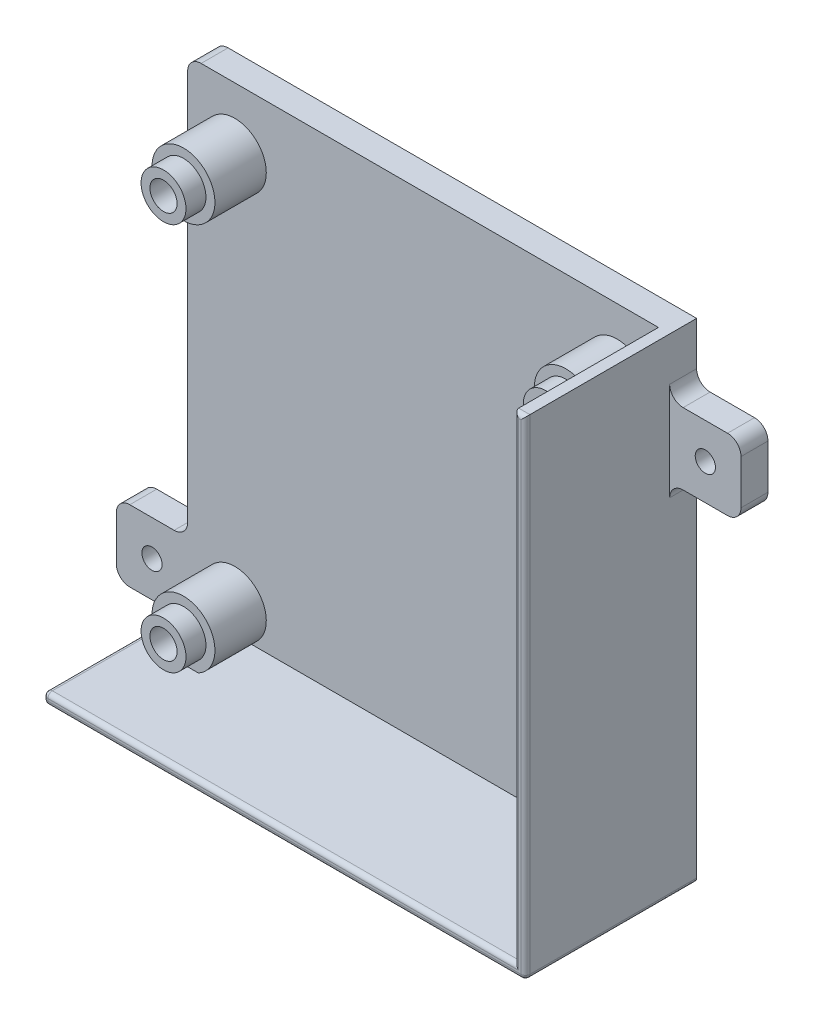
SolidWorks part; units mm, degrees
material "ABS"
ref_plane "X-Y Datum" through (0, 0, 0) normal (0, 0, 1) x (1, 0, 0)
ref_plane "X-Z Datum" through (0, 0, 0) normal (0, 1, 0) x (1, 0, 0)
ref_plane "Y-Z Datum" through (0, 0, 0) normal (1, 0, 0) x (0, 0, -1)
sketch "Sketch1" plane through (0, 0, 0) normal (0, 0, 1) x (1, 0, 0)
  line L1 (-52.3875, 53.1812) -> (52.3875, 53.1812)
  line L2 (-52.3875, 53.1812) -> (-52.3875, -53.1812)
  line L3 (-52.3875, -53.1812) -> (52.3875, -53.1812)
  line L4 (52.3875, 53.1812) -> (52.3875, -53.1812)
  line L5 (-52.3875, 53.1812) -> (52.3875, -53.1812) construction
  line L6 (-52.3875, -53.1812) -> (52.3875, 53.1812) construction
  point P0 (0, 0)
  dimension "D1" = 104.775
  dimension "D2" = 106.3625
extrude "Boss-Extrude1" add sketch "Sketch1" along normal blind 6
sketch "Sketch2" plane through (0, 0, 0) normal (0, 0, 1) x (1, 0, 0)
  line L3 (-52.3875, -53.1812) -> (-52.3875, -55.6812)
  line L4 (54.8875, 53.1812) -> (52.3875, 53.1812)
  line L5 (54.8875, -55.6812) -> (54.8875, 53.1812)
  line L6 (-52.3875, -55.6812) -> (54.8875, -55.6812)
  line L7 (54.8875, -55.6812) -> (54.8875, 53.1812)
  line L8 (-52.3875, -55.6812) -> (54.8875, -55.6812)
  line L9 (52.3875, -53.1812) -> (52.3875, 53.1812) construction
  line L10 (-52.3875, -53.1812) -> (52.3875, -53.1812) construction
  line L11 (52.3875, -53.1812) -> (52.3875, 53.1812)
  line L12 (-52.3875, -53.1812) -> (52.3875, -53.1812)
  dimension "D1" = 2.5
extrude "Boss-Extrude2" add sketch "Sketch2" along normal blind 38.1
sketch "Sketch3" plane through (0, 0, 6) normal (0, 0, 1) x (1, 0, 0)
  circle A0 centre (-41.882, 39.351) radius 3.025
  circle A1 centre (43.208, 39.351) radius 3.025
  circle A2 centre (43.208, -47.009) radius 3.025
  circle A3 centre (-41.882, -47.009) radius 3.025
  circle A4 centre (43.208, 39.351) radius 5
  circle A5 centre (-41.882, 39.351) radius 5
  circle A6 centre (-41.882, -47.009) radius 5
  circle A7 centre (43.208, -47.009) radius 5
  point P0 (-41.882, 39.351)
  point P1 (-41.882, -47.009)
  point P3 (43.208, -47.009)
  point P5 (43.208, 39.351)
  dimension "D1" = 6.05
  dimension "D2" = 10
extrude "Boss-Extrude3" add sketch "Sketch3" along normal blind 15.875
sketch "Sketch4" plane through (0, 0, 6) normal (0, 0, 1) x (1, 0, 0)
  circle A0 centre (43.208, 39.351) radius 7
  circle A1 centre (-41.882, 39.351) radius 7
  circle A2 centre (-41.882, -47.009) radius 7
  circle A3 centre (43.208, -47.009) radius 7
  circle A5 centre (-41.882, -47.009) radius 3.025
  circle A6 centre (-41.882, -47.009) radius 3.025
  circle A7 centre (43.208, -47.009) radius 3.025
  circle A8 centre (43.208, -47.009) radius 3.025
  circle A9 centre (43.208, 39.351) radius 3.025
  circle A10 centre (43.208, 39.351) radius 3.025
  circle A11 centre (-41.882, 39.351) radius 3.025
  circle A12 centre (-41.882, 39.351) radius 3.025
  dimension "D1" = 14
  dimension "D2" = 0
  dimension "D3" = 0
  dimension "D4" = 0
  dimension "D5" = 0
extrude "Boss-Extrude4" add sketch "Sketch4" along normal blind 11.43
sketch "Sketch6" plane through (0, 0, 0) normal (0, 0, 1) x (1, 0, 0)
  line L0 (-68.2625, -39.8062) -> (-52.3875, -55.6812)
  line L1 (-52.3875, -55.6812) -> (-68.2625, -55.6812)
  line L2 (-52.3875, -55.6812) -> (-52.3875, -39.8062)
  line L3 (-52.3875, -39.8062) -> (-68.2625, -39.8062)
  line L4 (-68.2625, -55.6812) -> (-68.2625, -39.8062)
  line L5 (54.8875, -55.6812) -> (54.8875, 53.1812) construction
  line L6 (54.8875, 40.4812) -> (70.7625, 40.4812)
  line L7 (54.8875, 40.4812) -> (54.8875, 24.6062)
  line L8 (54.8875, 24.6062) -> (70.7625, 24.6062)
  line L9 (70.7625, 40.4812) -> (70.7625, 24.6062)
  line L10 (54.8875, 24.6062) -> (70.7625, 40.4812)
  line L11 (54.8875, 53.1812) -> (52.3875, 53.1812) construction
  circle A0 centre (-60.325, -47.7437) radius 2 construction
  circle A1 centre (62.825, 32.5437) radius 2 construction
  dimension "D1" = 4
  dimension "D6" = 4
  dimension "D2" = 15.875
  dimension "D3" = 15.875
  dimension "D4" = 15.875
  dimension "D5" = 15.875
  dimension "D7" = 12.7
extrude "Boss-Extrude5" add sketch "Sketch6" along normal blind 6 contours L2 L3 L0 | L4 L1 L0 | L10 L8 L9 | L7 L10 L6
hole_wizard "M4 Clearance Hole1" positions "Sketch7" profile "Sketch8" hole size "M4" standard "ANSI Metric" end condition through all
sketch "Sketch7" plane through (0, 0, 6) normal (0, 0, 1) x (1, 0, 0)
  point P0 (62.825, 32.5437)
  point P3 (-60.325, -47.7437)
sketch "Sketch8" plane through (62.825, 32.5437, 6) normal (1, 0, 0) x (0, -1, 0)
  line L0 (0, 0) -> (0, 6)
  line L1 (0, 6) -> (2.25, 6)
  line L2 (2.25, 6) -> (2.25, 0)
  line L5 (2.25, 0) -> (0, 0)
  line L11 (0, -6.35) -> (0, 107.95) construction
  dimension "Thru Hole Dia." = 4.5
  dimension "Thru Hole Depth" = 6
fillet "Fillet2" radius 3 8 edges at (70.7625, 24.6062, 3) (70.7625, 40.4812, 3) (54.8875, 40.4812, 3) (54.8875, 24.6062, 3) (-68.2625, -55.6812, 3) (-68.2625, -39.8062, 3) (-52.3875, -39.8062, 3) (-52.3875, 53.1812, 3)
fillet "Fillet3" radius 1 9 edges at (52.3875, 0, 38.1) (53.6375, 53.1812, 38.1) (54.8875, -1.25, 38.1) (-52.3875, -54.4312, 38.1) (0, -53.1812, 38.1) (54.8875, -55.6812, 19.05) (1.25, -55.6812, 38.1) (-52.3875, -53.1812, 22.05) (-52.3875, -55.6812, 22.05)
